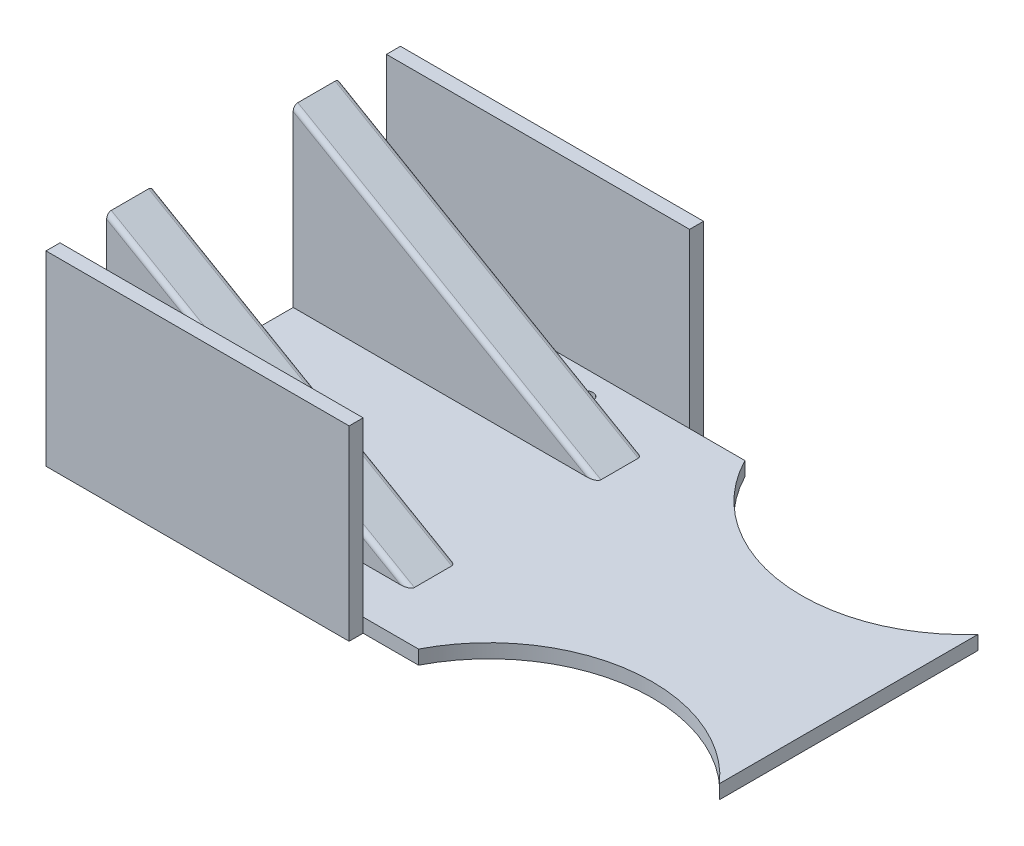
SolidWorks part; units mm, degrees
ref_plane "前视基准面" through (0, 0, 0) normal (0, 0, 1) x (1, 0, 0)
ref_plane "上视基准面" through (0, 0, 0) normal (0, 1, 0) x (1, 0, 0)
ref_plane "右视基准面" through (0, 0, 0) normal (1, 0, 0) x (0, 0, -1)
sketch "草图1" plane through (0, 0, 0) normal (0, 1, 0) x (1, 0, 0)
  line L0 (-92.9537, 0) -> (133.3808, 0) construction
  line L1 (0, 79.573) -> (0, -79.8577) construction
  line L2 (-82.7046, -35) -> (-82.7046, 35)
  line L3 (-82.7046, 35) -> (137.2954, 35)
  line L4 (137.2954, 35) -> (137.2954, -35)
  line L5 (-82.7046, -35) -> (137.2954, -35)
  point P10 (137.2954, 0)
  point P11 (-82.7046, 0)
  dimension "D1" = 70
  dimension "D2" = 220
extrude "凸台-拉伸1" add sketch "草图1" along normal blind 3
sketch "草图2" plane through (0, 0, 0) normal (0, 0, 1) x (1, 0, 0)
  line L0 (-2.7046, 3) -> (-2.7046, 43.2178) construction
  line L2 (59.2954, 3) -> (59.2954, 47.8617) construction
  line L3 (-82.7046, 3) -> (-82.7046, 0) construction
  line L5 (-82.7046, 40.5278) -> (-82.7046, 3)
  line L10 (-82.7046, 3) -> (-17.7046, 3)
  line L11 (-82.7046, 40.5278) -> (-17.7046, 3)
  dimension "D1" = 62
  dimension "D2" = 80
  dimension "D3" = 30
  dimension "D4" = 65
extrude "凸台-拉伸2" add sketch "草图2" along normal blind 25 and the other way blind 25
sketch "草图6" plane through (-82.7046, 0, 0) normal (-1, 0, 0) x (0, 0, 1)
  line L0 (0, 40.5278) -> (0, 0) construction
  line L1 (-25, 40.5278) -> (25, 40.5278) construction
  line L2 (-15, 40.5278) -> (-15, 3)
  line L3 (-15, 3) -> (15, 3)
  line L4 (15, 3) -> (15, 40.5278)
  line L5 (15, 40.5278) -> (-15, 40.5278)
  dimension "D1" = 15
  dimension "D2" = 15
extrude "切除-拉伸4" cut sketch "草图6" against normal through all
ref_plane "基准面1" through (-87.2964, 23.391, 0) normal (-0.9659, 0.2588, 0) x (0, 0, 1)
sketch "草图7" plane through (0, 3, 0) normal (0, 1, 0) x (1, 0, 0)
  line L0 (-2.7046, 35) -> (-2.7046, -35) construction
  line L4 (137.2954, 35) -> (-82.7046, 35) construction
  line L5 (-82.7046, -35) -> (137.2954, -35) construction
  line L6 (-82.7046, 35) -> (-82.7046, 25) construction
  line L7 (53.2954, 35) -> (53.2954, -35) construction
  line L8 (25.2954, 88.1076) -> (25.2954, -100.7895) construction
  line L9 (-82.7046, 0) -> (117.2954, 0) construction
  line L11 (-82.7046, 15) -> (-82.7046, -15) construction
  circle A0 centre (25.2954, 51) radius 35
  circle A1 centre (25.2954, -51) radius 35
  dimension "D4" = 70
  dimension "D1" = 80
  dimension "D2" = 56
  dimension "D3" = 28
  dimension "D5" = 102
extrude "切除-拉伸5" cut sketch "草图7" against normal through all
sketch "草图8" plane through (-82.7046, 0, 0) normal (-1, 0, 0) x (0, 0, 1)
  line L0 (35, 0) -> (35, 40)
  line L1 (35, 40) -> (38, 40)
  line L2 (38, 40) -> (38, 0)
  line L3 (38, 0) -> (35, 0)
  line L4 (0, 36.5043) -> (0, -13.2047) construction
  line L5 (-38, 0) -> (-35, 0)
  line L6 (-38, 40) -> (-38, 0)
  line L7 (-35, 40) -> (-38, 40)
  line L8 (-35, 0) -> (-35, 40)
  dimension "D1" = 3
  dimension "D2" = 40
extrude "凸台-拉伸3" add sketch "草图8" against normal blind 65
sketch "草图9" plane through (0, 3, 0) normal (0, 1, 0) x (1, 0, 0)
  line L0 (-82.7046, 15) -> (-82.7046, -15) construction
  line L1 (-82.7046, 0) -> (117.2954, 0) construction
  circle A0 centre (-74.7668, 29.8601) radius 1.5
  circle A1 centre (-54.7668, 29.8601) radius 1.5
  circle A2 centre (-34.7668, 29.8601) radius 1.5
  circle A3 centre (-34.7668, -29.8601) radius 1.5
  circle A4 centre (-54.7668, -29.8601) radius 1.5
  circle A5 centre (-74.7668, -29.8601) radius 1.5
  circle A12 centre (68.0316, 22) radius 1.5
  circle A13 centre (88.0316, 22) radius 1.5
  circle A14 centre (108.0316, 22) radius 1.5
  circle A15 centre (108.0316, -22) radius 1.5
  circle A16 centre (88.0316, -22) radius 1.5
  circle A17 centre (68.0316, -22) radius 1.5
  circle A18 centre (128.0316, 22) radius 1.5
  circle A19 centre (128.0316, -22) radius 1.5
  dimension "D1" = 3
  dimension "D3" = 22
  dimension "D5" = 3
  dimension "D7" = 3
  dimension "D9" = 3
  dimension "D4" = 20
  dimension "D8" = 20
  dimension "D2" = 3
  dimension "D6" = 3
extrude "切除-拉伸6" cut sketch "草图9" against normal through all
fillet "圆角5" radius 1 4 edges at (-50.2046, 21.7639, -15) (-50.2046, 21.7639, 15) (-50.2046, 21.7639, 25) (-50.2046, 21.7639, -25)
sketch "草图10" plane through (0, 3, 0) normal (0, 1, 0) x (1, 0, 0)
  line L0 (-82.7046, 0) -> (137.2954, 0) construction
  line L1 (-82.7046, 15) -> (-82.7046, -15) construction
  line L2 (137.2954, 35) -> (137.2954, -35) construction
  line L3 (-82.7046, -10) -> (-82.7046, 10)
  line L4 (-82.7046, 10) -> (-17.7046, 10)
  line L5 (-17.7046, 10) -> (-17.7046, -10)
  line L6 (-82.7046, -10) -> (-17.7046, -10)
  point P11 (-17.7046, 0)
  dimension "D1" = 20
sketch "草图12" plane through (0, 3, 0) normal (0, 1, 0) x (1, 0, 0)
  line L2 (51.4241, 0) -> (51.4241, 45.1417)
  line L3 (51.4241, 45.1417) -> (51.4241, -42.9308)
  line L6 (51.4241, 45.1417) -> (162.1112, 35)
  line L7 (162.1112, 35) -> (165.9627, -47.0392)
  line L8 (165.9627, -47.0392) -> (51.4241, -42.9308)
  arc M13 (-5.8334, -35) -> (56.4241, -35) centre (25.2954, -51) cw
  line M14 (56.4241, -35) -> (137.2954, -35)
  line M15 (137.2954, -35) -> (137.2954, 35)
  line M16 (137.2954, 35) -> (56.4241, 35)
  arc M17 (56.4241, 35) -> (-5.8334, 35) centre (25.2954, 51) cw
  circle M27 centre (68.0316, 22) radius 1.5
  circle M28 centre (128.0316, -22) radius 1.5
  circle M32 centre (128.0316, 22) radius 1.5
  circle M35 centre (88.0316, 22) radius 1.5
  circle M36 centre (108.0316, 22) radius 1.5
  circle M37 centre (108.0316, -22) radius 1.5
  circle M38 centre (88.0316, -22) radius 1.5
  circle M39 centre (68.0316, -22) radius 1.5
extrude "切除-拉伸8" cut sketch "草图12" against normal through all contours L2 L3 M13 M14 M15 M16 M17 M28 M32 M36 M38 M39 M37 M35 M27
